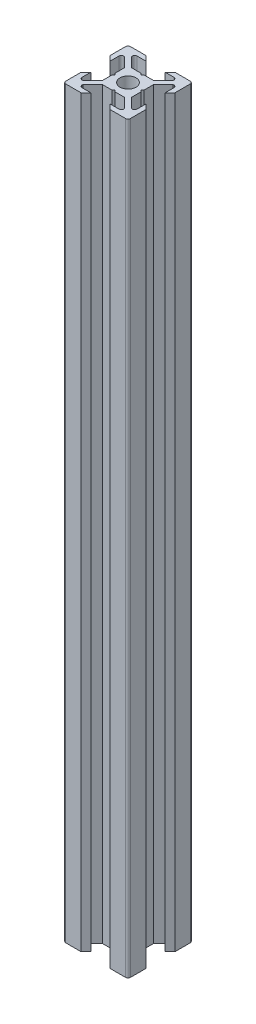
SolidWorks part; units mm, degrees
ref_plane "Face" through (0, 0, 0) normal (0, 0, 1) x (1, 0, 0)
ref_plane "Dessus" through (0, 0, 0) normal (0, 1, 0) x (1, 0, 0)
ref_plane "Droite" through (0, 0, 0) normal (1, 0, 0) x (0, 0, -1)
sketch "Esquisse1" plane through (0, 0, 0) normal (0, 1, 0) x (1, 0, 0)
  line L0 (0, 0) -> (0, 10) construction
  line L1 (0, 0) -> (-10, 0) construction
  line L2 (-10, 0) -> (-10, 10) construction
  line L3 (-10, 10) -> (0, 10) construction
  line L4 (0, 4) -> (-0.5, 4.5)
  line L5 (-0.5, 4.5) -> (-3.4393, 4.5)
  line L6 (-3.4393, 4.5) -> (-6.4393, 7.5)
  line L7 (-6.4393, 7.5) -> (-6.4393, 8.5)
  line L8 (-6.4393, 8.5) -> (-3, 8.5)
  line L9 (-3, 8.5) -> (-4.5, 10)
  line L10 (-4.5, 10) -> (-10, 10)
  line L11 (0, 0) -> (-10, 10) construction
  line L12 (-10, 4.5) -> (-10, 10)
  line L13 (-8.5, 3) -> (-10, 4.5)
  line L14 (-8.5, 6.4393) -> (-8.5, 3)
  line L15 (-7.5, 6.4393) -> (-8.5, 6.4393)
  line L16 (-4.5, 3.4393) -> (-7.5, 6.4393)
  line L17 (-4.5, 0.5) -> (-4.5, 3.4393)
  line L18 (-4, 0) -> (-4.5, 0.5)
  line L19 (0, -4) -> (-0.5, -4.5)
  line L20 (-0.5, -4.5) -> (-3.4393, -4.5)
  line L21 (-4, 0) -> (-4.5, -0.5)
  line L22 (-4.5, -0.5) -> (-4.5, -3.4393)
  line L23 (-4.5, -3.4393) -> (-7.5, -6.4393)
  line L24 (-3.4393, -4.5) -> (-6.4393, -7.5)
  line L25 (-3, -8.5) -> (-4.5, -10)
  line L26 (-6.4393, -8.5) -> (-3, -8.5)
  line L27 (-6.4393, -7.5) -> (-6.4393, -8.5)
  line L28 (-7.5, -6.4393) -> (-8.5, -6.4393)
  line L29 (-4.5, -10) -> (-10, -10)
  line L30 (-10, -4.5) -> (-10, -10)
  line L31 (-8.5, -3) -> (-10, -4.5)
  line L32 (-8.5, -6.4393) -> (-8.5, -3)
  line L33 (8.5, -6.4393) -> (8.5, -3)
  line L34 (8.5, -3) -> (10, -4.5)
  line L35 (10, -4.5) -> (10, -10)
  line L36 (4.5, -10) -> (10, -10)
  line L37 (7.5, -6.4393) -> (8.5, -6.4393)
  line L38 (6.4393, -7.5) -> (6.4393, -8.5)
  line L39 (6.4393, -8.5) -> (3, -8.5)
  line L40 (3, -8.5) -> (4.5, -10)
  line L41 (3.4393, -4.5) -> (6.4393, -7.5)
  line L42 (4.5, -3.4393) -> (7.5, -6.4393)
  line L43 (4.5, -0.5) -> (4.5, -3.4393)
  line L44 (4, 0) -> (4.5, -0.5)
  line L45 (0.5, -4.5) -> (3.4393, -4.5)
  line L46 (0, -4) -> (0.5, -4.5)
  line L47 (4, 0) -> (4.5, 0.5)
  line L48 (4.5, 0.5) -> (4.5, 3.4393)
  line L49 (4.5, 3.4393) -> (7.5, 6.4393)
  line L50 (7.5, 6.4393) -> (8.5, 6.4393)
  line L51 (8.5, 6.4393) -> (8.5, 3)
  line L52 (8.5, 3) -> (10, 4.5)
  line L53 (10, 4.5) -> (10, 10)
  line L54 (4.5, 10) -> (10, 10)
  line L55 (3, 8.5) -> (4.5, 10)
  line L56 (6.4393, 8.5) -> (3, 8.5)
  line L57 (6.4393, 7.5) -> (6.4393, 8.5)
  line L58 (3.4393, 4.5) -> (6.4393, 7.5)
  line L59 (0.5, 4.5) -> (3.4393, 4.5)
  line L60 (0, 4) -> (0.5, 4.5)
  circle A0 centre (0, 0) radius 2.5
  dimension "D10" = 5
  dimension "D1" = 10
  dimension "D2" = 45
  dimension "D3" = 45
  dimension "D4" = 1.5
  dimension "D5" = 7
  dimension "D6" = 1
  dimension "D7" = 4.5
  dimension "D8" = 0.5
  dimension "D9" = 0.75
extrude "Extrusion1" add sketch "Esquisse1" along normal blind 230
fillet "Congé1" radius 0.75 12 edges at (-8.5, 115, -6.4393) (-6.4393, 115, -8.5) (8.5, 115, -6.4393) (6.4393, 115, -8.5) (-8.5, 115, 6.4393) (-6.4393, 115, 8.5) (8.5, 115, 6.4393) (6.4393, 115, 8.5) (10, 115, -10) (-10, 115, -10) (-10, 115, 10) (10, 115, 10)
